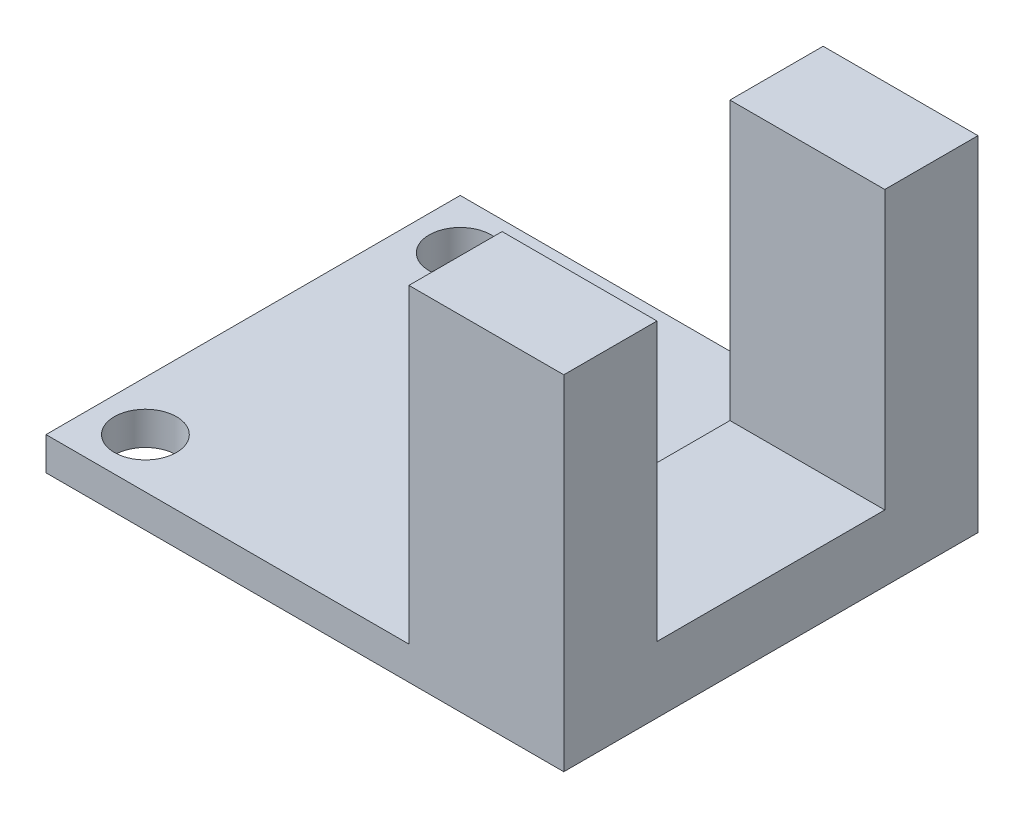
SolidWorks part; units mm, degrees
ref_plane "Front Plane" through (0, 0, 0) normal (0, 0, 1) x (1, 0, 0)
ref_plane "Top Plane" through (0, 0, 0) normal (0, 1, 0) x (1, 0, 0)
ref_plane "Right Plane" through (0, 0, 0) normal (1, 0, 0) x (0, 0, -1)
sketch "Sketch1" plane through (0, 0, 0) normal (0, 1, 0) x (1, 0, 0)
  line L1 (-12.5, 10) -> (12.5, 10)
  line L2 (-12.5, 10) -> (-12.5, -10)
  line L3 (-12.5, -10) -> (12.5, -10)
  line L4 (12.5, 10) -> (12.5, -10)
  line L5 (-12.5, 10) -> (12.5, -10) construction
  line L6 (-12.5, -10) -> (12.5, 10) construction
  point P0 (0, 0)
  dimension "D1" = 25
  dimension "D2" = 20
extrude "Boss-Extrude1" add sketch "Sketch1" along normal blind 1.6
sketch "Sketch2" plane through (0, 1.6, 0) normal (0, 1, 0) x (1, 0, 0)
  line L0 (-12.5, -10) -> (12.5, -10) construction
  line L1 (12.5, 10) -> (5.0229, 10)
  line L2 (12.5, 10) -> (12.5, -10)
  line L3 (12.5, -10) -> (5.0229, -10)
  line L4 (5.0229, 10) -> (5.0229, -10)
extrude "Boss-Extrude2" add sketch "Sketch2" along normal blind 15
sketch "Sketch3" plane through (12.5, 0, 0) normal (1, 0, 0) x (0, 0, -1)
  line L0 (-10, 16.6) -> (10, 16.6) construction
  line L1 (-5.5, 16.6) -> (5.5, 16.6)
  line L2 (-5.5, 16.6) -> (-5.5, 3.1976)
  line L3 (-5.5, 3.1976) -> (5.5, 3.1976)
  line L4 (5.5, 16.6) -> (5.5, 3.1976)
  line L5 (-10, 16.6) -> (-10, 0) construction
  line L6 (10, 16.6) -> (10, 0) construction
  dimension "D1" = 4.5
  dimension "D2" = 4.5
extrude "Cut-Extrude1" cut sketch "Sketch3" against normal blind 15
sketch "Sketch4" plane through (0, 1.6, 0) normal (0, 1, 0) x (1, 0, 0)
  line L0 (-10.1, 10) -> (-10.1, -10) construction
  line L1 (5.0229, 10) -> (-12.5, 10) construction
  line L2 (-12.5, -10) -> (5.0229, -10) construction
  line L3 (-12.5, 10) -> (-12.5, -10) construction
  circle A0 centre (-10.1, 7.6) radius 1.5
  circle A1 centre (-10.1, -7.6) radius 1.5
  dimension "D4" = 3
  dimension "D5" = 3
  dimension "D1" = 2.4
  dimension "D2" = 2.4
  dimension "D3" = 2.4
extrude "Cut-Extrude2" cut sketch "Sketch4" against normal blind 15
